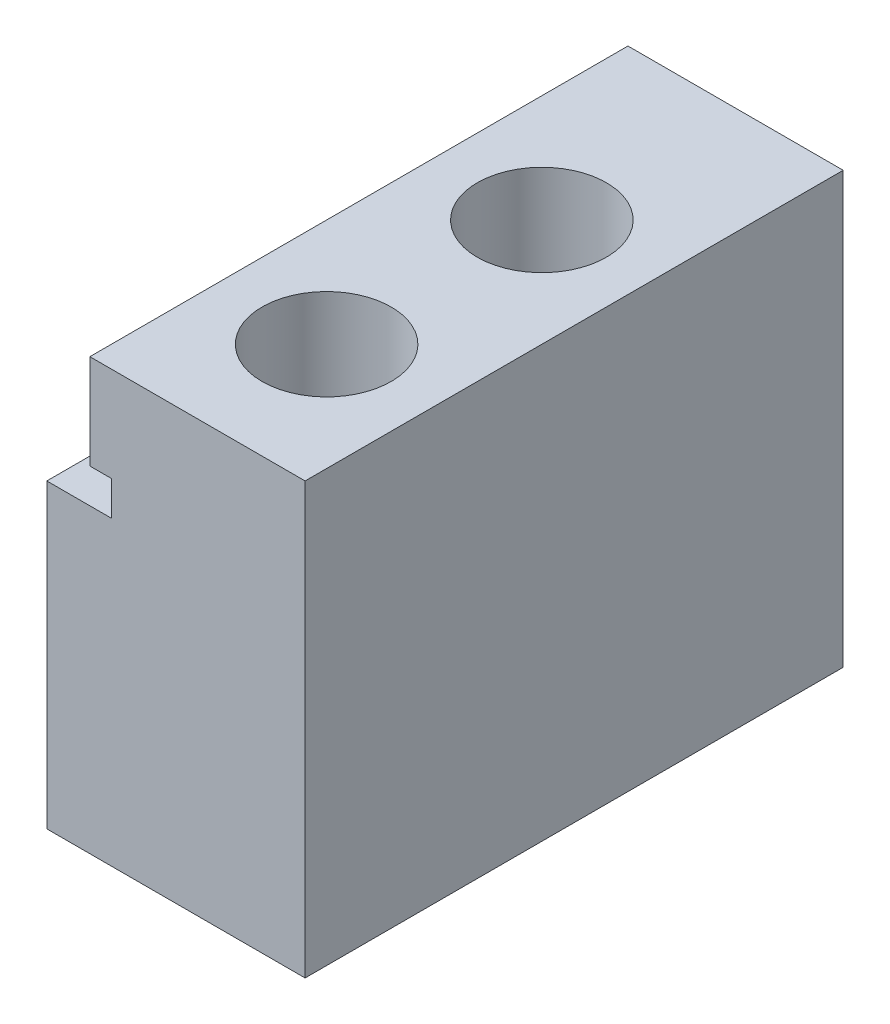
SolidWorks part; units mm, degrees
material "ПВХ Жесткий"
ref_plane "Спереди" through (0, 0, 0) normal (0, 0, 1) x (1, 0, 0)
ref_plane "Сверху" through (0, 0, 0) normal (0, 1, 0) x (1, 0, 0)
ref_plane "Справа" through (0, 0, 0) normal (1, 0, 0) x (0, 0, -1)
sketch "Эскиз1" plane through (0, 0, 0) normal (0, 1, 0) x (1, 0, 0)
  line L1 (0, 0) -> (12, 0)
  line L2 (0, 0) -> (0, 25)
  line L3 (0, 25) -> (12, 25)
  line L4 (12, 0) -> (12, 25)
  circle A0 centre (7, 6) radius 1.75
  circle A1 centre (7, 16) radius 1.75
  dimension "D3" = 10
  dimension "D5" = 6
  dimension "D6" = 3.5
  dimension "D1" = 25
  dimension "D2" = 12
  dimension "D4" = 7
extrude "Бобышка-Вытянуть1" add sketch "Эскиз1" along normal blind 20
sketch "Эскиз2" plane through (0, 0, 0) normal (0, 0, 1) x (1, 0, 0)
  line L0 (0, 14) -> (3, 14)
  line L1 (0, 20) -> (0, 0) construction
  line L2 (3, 14) -> (3, 15.6)
  line L3 (3, 15.6) -> (2, 15.6)
  line L4 (2, 15.6) -> (2, 20)
  line L5 (0, 20) -> (12, 20) construction
  line L6 (0, 0) -> (12, 0) construction
  dimension "D1" = 14
  dimension "D2" = 1.6
  dimension "D3" = 1
  dimension "D4" = 2
extrude "Вырез-Вытянуть1" cut sketch "Эскиз2" against normal through all
sketch "Эскиз3" plane through (0, 20, 0) normal (0, 1, 0) x (1, 0, 0)
  circle A0 centre (7, 16) radius 3
  circle A1 centre (7, 6) radius 3
  dimension "D1" = 6
extrude "Вырез-Вытянуть2" cut sketch "Эскиз3" against normal blind 10
sketch "Эскиз4" plane through (0, 0, 0) normal (0, -1, 0) x (1, 0, 0)
  circle A0 centre (7, -16) radius 3.75
  circle A1 centre (7, -6) radius 3.75
  dimension "D1" = 7.5
extrude "Вырез-Вытянуть3" cut sketch "Эскиз4" against normal blind 3
